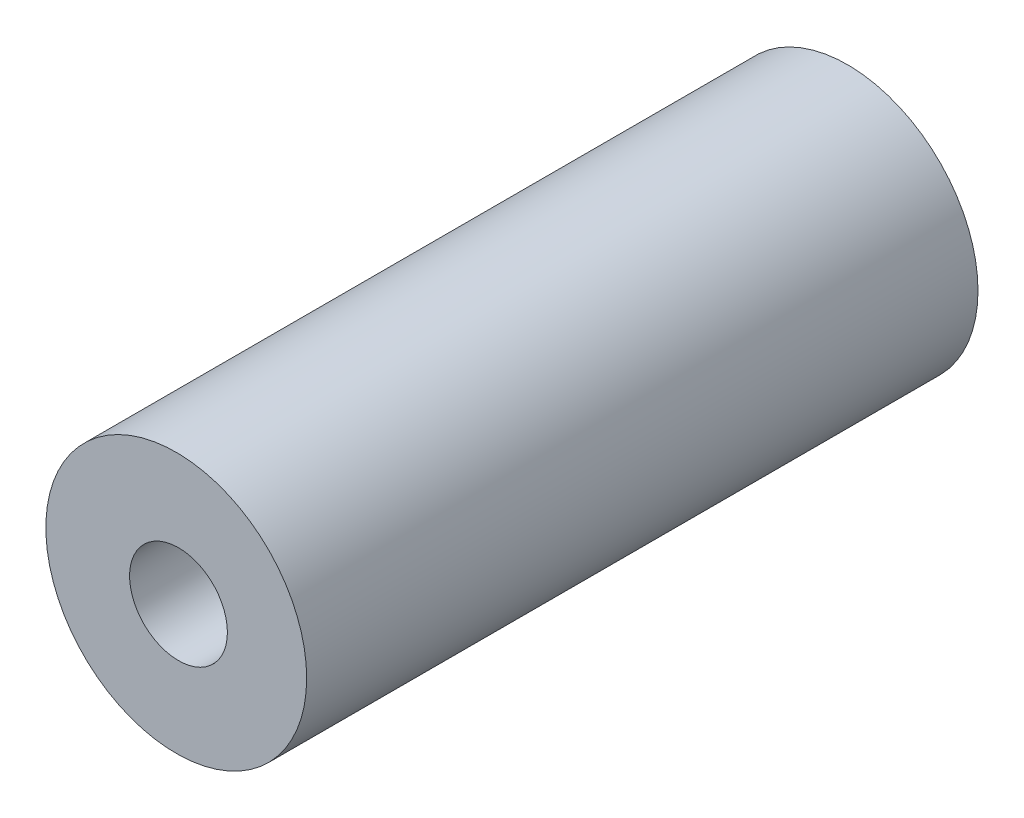
SolidWorks part; units mm, degrees
material "Plastique personnalisé"
ref_plane "Plan de face" through (0, 0, 0) normal (0, 0, 1) x (1, 0, 0)
ref_plane "Plan de dessus" through (0, 0, 0) normal (0, 1, 0) x (1, 0, 0)
ref_plane "Plan de droite" through (0, 0, 0) normal (1, 0, 0) x (0, 0, -1)
sketch "Esquisse1" plane through (0, 0, 0) normal (0, 0, 1) x (1, 0, 0)
  circle A0 centre (0, 0) radius 1.5
  circle A1 centre (-0.0686, 0) radius 4
  dimension "D1" = 8
  dimension "D2" = 3
extrude "Boss.-Extru.1" add sketch "Esquisse1" along normal blind 20.59
